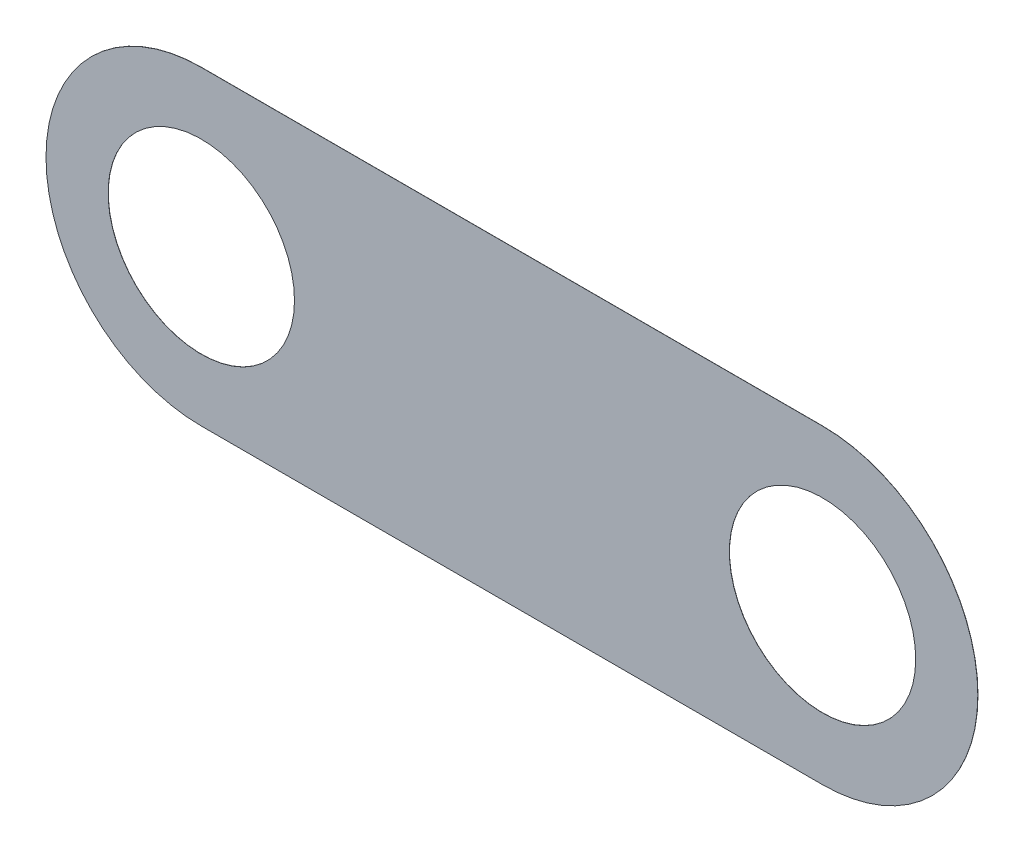
SolidWorks part; units mm, degrees
ref_plane "Płaszczyzna przednia" through (0, 0, 0) normal (0, 0, 1) x (1, 0, 0)
ref_plane "Płaszczyzna górna" through (0, 0, 0) normal (0, 1, 0) x (1, 0, 0)
ref_plane "Płaszczyzna prawa" through (0, 0, 0) normal (1, 0, 0) x (0, 0, -1)
sketch "Szkic1" plane through (0, 0, 0) normal (0, 0, 1) x (1, 0, 0)
  line L2 (0, 0) -> (40, 0) construction
  line L3 (0, 10) -> (40, 10)
  line L4 (0, -10) -> (40, -10)
  circle A0 centre (0, 0) radius 6
  circle A1 centre (40, 0) radius 6
  arc A4 (0, 10) -> (0, -10) centre (0, 0) ccw
  arc A5 (40, -10) -> (40, 10) centre (40, 0) ccw
  point P5 (20, 0)
  dimension "D1" = 40
  dimension "D2" = 12
  dimension "D3" = 12
  dimension "D4" = 20
extrude "Dodanie-wyciągnięcie1" add sketch "Szkic1" along normal blind 0.01
